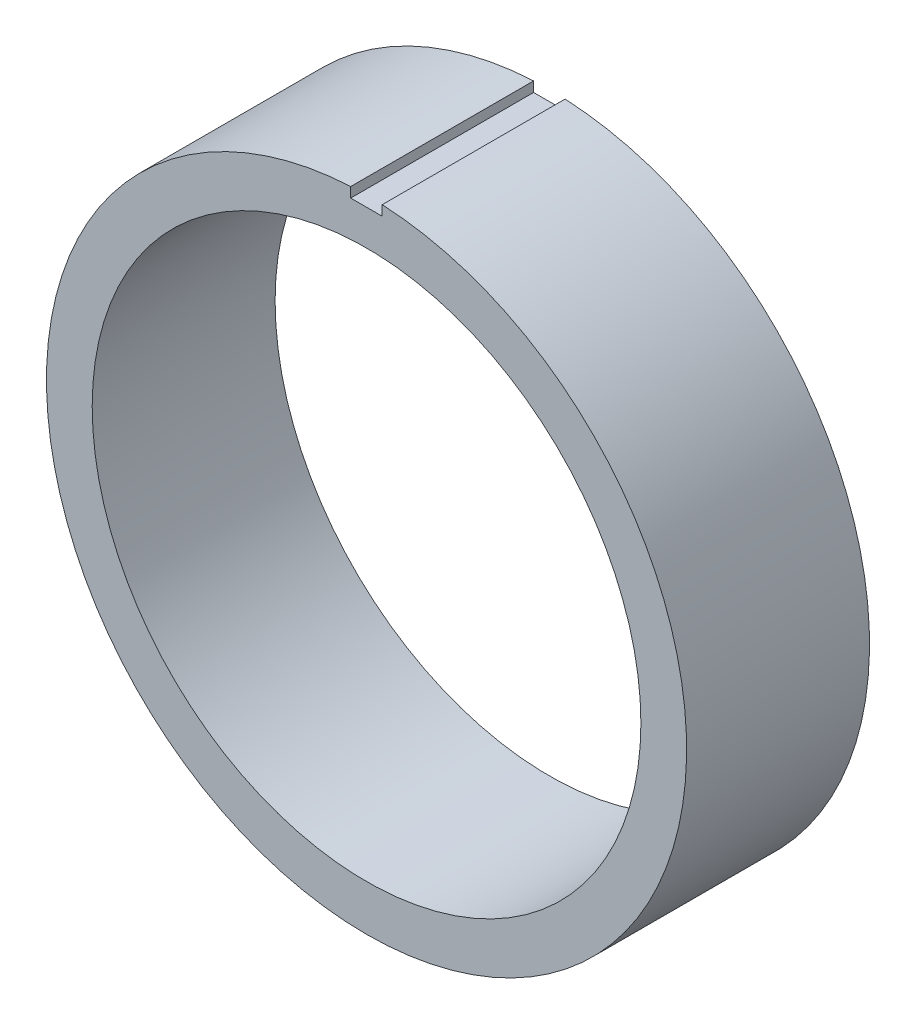
SolidWorks part; units mm, degrees
ref_plane "Front Plane" through (0, 0, 0) normal (0, 0, 1) x (1, 0, 0)
ref_plane "Top Plane" through (0, 0, 0) normal (0, 1, 0) x (1, 0, 0)
ref_plane "Right Plane" through (0, 0, 0) normal (1, 0, 0) x (0, 0, -1)
sketch "Sketch1" plane through (0, 0, 0) normal (0, 0, 1) x (1, 0, 0)
  circle A0 centre (0, 0) radius 12
  circle A1 centre (0, 0) radius 14
  dimension "D1" = 24
  dimension "D2" = 2
extrude "Boss-Extrude1" add sketch "Sketch1" along normal blind 8
sketch "Sketch2" plane through (0, 0, 8) normal (0, 0, 1) x (1, 0, 0)
  line L1 (-0.6927, 14.3623) -> (0.6843, 14.3623)
  line L2 (-0.6927, 14.3623) -> (-0.6927, 13.5448)
  line L3 (-0.6927, 13.5448) -> (0.6843, 13.5448)
  line L4 (0.6843, 14.3623) -> (0.6843, 13.5448)
extrude "Cut-Extrude1" cut sketch "Sketch2" against normal blind 10
